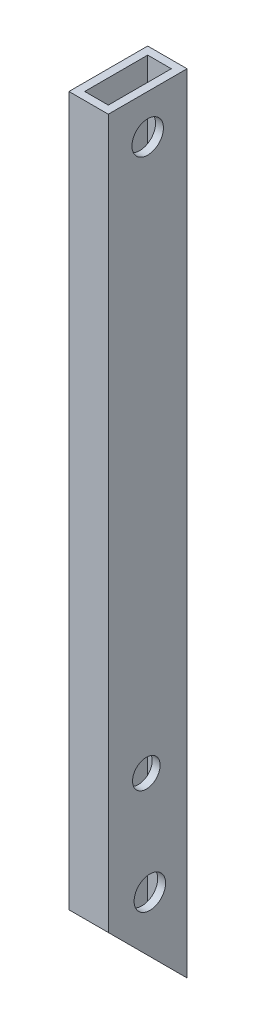
SolidWorks part; units mm, degrees
ref_plane "Front Plane" through (0, 0, 0) normal (0, 0, 1) x (1, 0, 0)
ref_plane "Top Plane" through (0, 0, 0) normal (0, 1, 0) x (1, 0, 0)
ref_plane "Right Plane" through (0, 0, 0) normal (1, 0, 0) x (0, 0, -1)
sketch "Sketch1" plane through (0, 0, 0) normal (0, 0, 1) x (1, 0, 0)
  line L1 (-5, 100) -> (5, 100)
  line L2 (-5, 100) -> (-5, -100)
  line L3 (-5, -100) -> (5, -100)
  line L4 (5, 100) -> (5, -100)
  line L5 (-5, 100) -> (5, -100) construction
  line L6 (-5, -100) -> (5, 100) construction
  point P0 (0, 0)
  dimension "D1" = 10
  dimension "D2" = 200
extrude "Boss-Extrude1" add sketch "Sketch1" along normal blind 20
shell "Shell1" thickness 2
sketch "Sketch2" plane through (-5, 0, 0) normal (-1, 0, 0) x (0, 0, 1)
  line L0 (0, -100) -> (20, -80)
  line L1 (20, 100) -> (20, -100) construction
  line L2 (20, -80) -> (20, -100)
  line L3 (20, -100) -> (0, -100)
  dimension "D1" = 45
extrude "Cut-Extrude1" cut sketch "Sketch2" against normal blind 10
sketch "Sketch4" plane through (5, 0, 0) normal (1, 0, 0) x (0, 0, -1)
  line L0 (-20, 100) -> (-20, -80) construction
  line L2 (-20, 100) -> (0, 100) construction
  circle A0 centre (-10, 90) radius 4
  dimension "D3" = 8
  dimension "D1" = 10
  dimension "D2" = 10
extrude "Cut-Extrude3" cut sketch "Sketch4" against normal blind 10
sketch "Sketch5" plane through (5, 0, 0) normal (1, 0, 0) x (0, 0, -1)
  circle A0 centre (-9.4533, -76.4045) radius 4
  circle A1 centre (-10.3472, -49.772) radius 3.5
  point P6 (0, 0)
  point P7 (0, 0)
  dimension "D1" = 7
extrude "Cut-Extrude4" cut sketch "Sketch5" against normal blind 10
